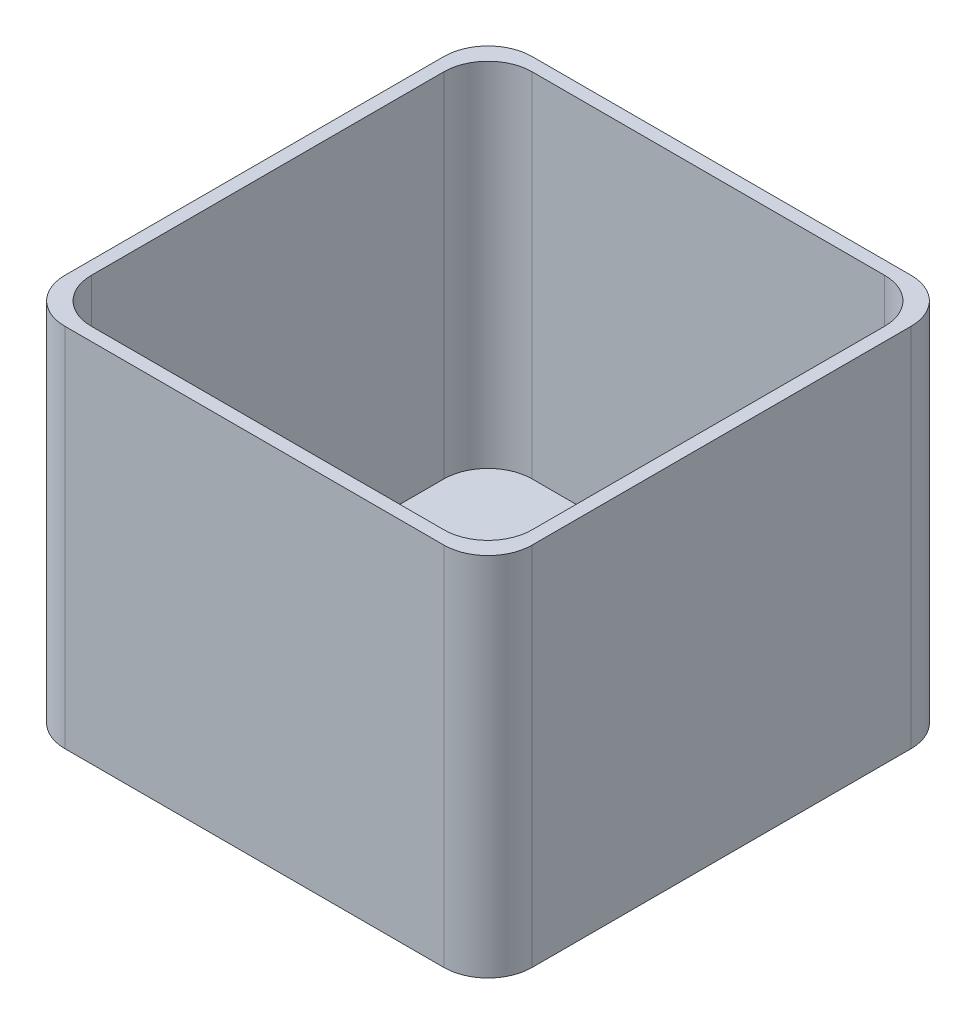
SolidWorks part; units mm, degrees
ref_plane "Front Plane" through (0, 0, 0) normal (0, 0, 1) x (1, 0, 0)
ref_plane "Top Plane" through (0, 0, 0) normal (0, 1, 0) x (1, 0, 0)
ref_plane "Right Plane" through (0, 0, 0) normal (1, 0, 0) x (0, 0, -1)
sketch "Sketch1" plane through (0, 0, 0) normal (0, 1, 0) x (1, 0, 0)
  line L1 (-73.8782, -84.6421) -> (12.1218, -84.6421)
  line L2 (-83.8782, -74.6421) -> (-83.8782, 11.3579)
  line L3 (-73.8782, 21.3579) -> (12.1218, 21.3579)
  line L4 (22.1218, -74.6421) -> (22.1218, 11.3579)
  line L5 (-83.8782, -84.6421) -> (22.1218, 21.3579) construction
  line L6 (-83.8782, 21.3579) -> (22.1218, -84.6421) construction
  line L7 (-70.8782, -81.6421) -> (9.1218, -81.6421)
  line L8 (-80.8782, -71.6421) -> (-80.8782, 8.3579)
  line L9 (-70.8782, 18.3579) -> (9.1218, 18.3579)
  line L10 (19.1218, -71.6421) -> (19.1218, 8.3579)
  line L11 (-80.8782, -81.6421) -> (19.1218, 18.3579) construction
  line L12 (-80.8782, 18.3579) -> (19.1218, -81.6421) construction
  arc A0 (12.1218, 21.3579) -> (22.1218, 11.3579) centre (12.1218, 11.3579) cw
  arc A1 (12.1218, -84.6421) -> (22.1218, -74.6421) centre (12.1218, -74.6421) ccw
  arc A2 (-73.8782, -84.6421) -> (-83.8782, -74.6421) centre (-73.8782, -74.6421) cw
  arc A3 (-83.8782, 11.3579) -> (-73.8782, 21.3579) centre (-73.8782, 11.3579) cw
  arc A4 (9.1218, -81.6421) -> (19.1218, -71.6421) centre (9.1218, -71.6421) ccw
  arc A5 (-70.8782, -81.6421) -> (-80.8782, -71.6421) centre (-70.8782, -71.6421) cw
  arc A6 (-80.8782, 8.3579) -> (-70.8782, 18.3579) centre (-70.8782, 8.3579) cw
  arc A7 (9.1218, 18.3579) -> (19.1218, 8.3579) centre (9.1218, 8.3579) cw
  circle A8 centre (14.7274, -68.4363) radius 4.3944
  point P0 (-30.8782, -31.6421)
  point P17 (-30.8782, -31.6421)
  dimension "D3" = 10
  dimension "D6" = 10
  dimension "D1" = 106
  dimension "D2" = 106
  dimension "D4" = 100
  dimension "D5" = 100
extrude "Boss-Extrude1" add sketch "Sketch1" along normal blind 80 contours A3 L2 A2 L1 A1 L4 A0 L3 L9 A7 L10 A4 L7 A5 L8 A6
sketch "Sketch2" plane through (0, 0, 0) normal (0, -1, 0) x (1, 0, 0)
  line L0 (9.1218, 81.6421) -> (-70.8782, 81.6421)
  line L7 (-73.983, -21.3579) -> (12.2266, -21.3579)
  line L8 (-83.983, -11.3579) -> (-83.983, 74.6421)
  line L9 (-73.983, 84.6421) -> (12.2266, 84.6421)
  line L10 (22.2266, -11.3579) -> (22.2266, 74.6421)
  line L11 (-83.983, -21.3579) -> (22.2266, 84.6421) construction
  line L12 (-83.983, 84.6421) -> (22.2266, -21.3579) construction
  arc A0 (12.2266, -21.3579) -> (22.2266, -11.3579) centre (12.2266, -11.3579) ccw
  arc A1 (-73.983, -21.3579) -> (-83.983, -11.3579) centre (-73.983, -11.3579) cw
  arc A2 (-83.983, 74.6421) -> (-73.983, 84.6421) centre (-73.983, 74.6421) cw
  arc A3 (12.2266, 84.6421) -> (22.2266, 74.6421) centre (12.2266, 74.6421) cw
  circle A4 centre (13.9687, -4.778) radius 4.778
  point P14 (-30.8782, 31.6421)
  arc M9 (-83.8782, -11.3579) -> (-73.8782, -21.3579) centre (-73.8782, -11.3579) ccw
  line M10 (-73.8782, -21.3579) -> (12.1218, -21.3579)
  arc M11 (12.1218, -21.3579) -> (22.1218, -11.3579) centre (12.1218, -11.3579) ccw
  line M12 (22.1218, -11.3579) -> (22.1218, 74.6421)
  arc M13 (22.1218, 74.6421) -> (12.1218, 84.6421) centre (12.1218, 74.6421) ccw
  line M14 (12.1218, 84.6421) -> (-73.8782, 84.6421)
  arc M15 (-73.8782, 84.6421) -> (-83.8782, 74.6421) centre (-73.8782, 74.6421) ccw
  line M16 (-83.8782, 74.6421) -> (-83.8782, -11.3579)
  line M17 (9.1218, -18.3579) -> (-70.8782, -18.3579)
  arc M18 (-70.8782, -18.3579) -> (-80.8782, -8.3579) centre (-70.8782, -8.3579) cw
  line M19 (-80.8782, -8.3579) -> (-80.8782, 71.6421)
  arc M20 (-80.8782, 71.6421) -> (-70.8782, 81.6421) centre (-70.8782, 71.6421) cw
  line M21 (-70.8782, 81.6421) -> (9.1218, 81.6421)
  arc M22 (9.1218, 81.6421) -> (19.1218, 71.6421) centre (9.1218, 71.6421) cw
  line M23 (19.1218, 71.6421) -> (19.1218, -8.3579)
  arc M24 (19.1218, -8.3579) -> (9.1218, -18.3579) centre (9.1218, -8.3579) cw
  dimension "D2" = 10
  dimension "D1" = 106
extrude "Boss-Extrude4" add sketch "Sketch2" along normal blind 3 contours A4 M17 M24 M23 M22 M21 M20 M19 M18 | M16 M9 M10 M11 M12 M13 M14 M15 M24 M17 M18 M19 M20 M21 M22 M23
